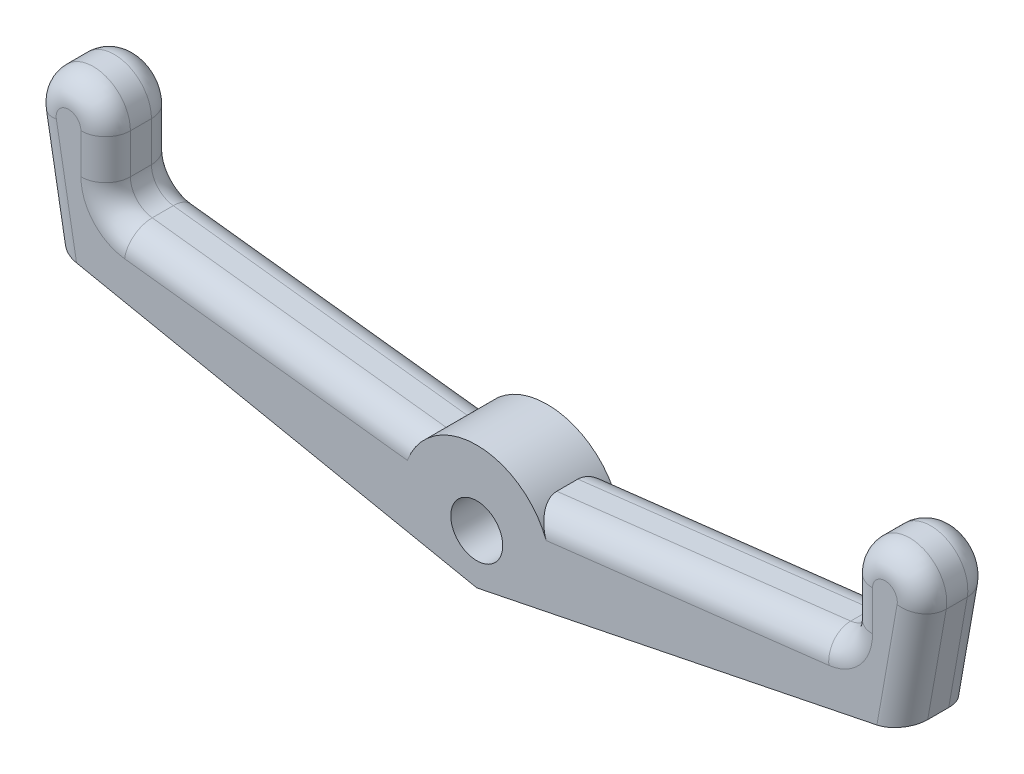
SolidWorks part; units mm, degrees
ref_plane "Front Plane" through (0, 0, 0) normal (0, 0, 1) x (1, 0, 0)
ref_plane "Top Plane" through (0, 0, 0) normal (0, 1, 0) x (1, 0, 0)
ref_plane "Right Plane" through (0, 0, 0) normal (1, 0, 0) x (0, 0, -1)
sketch "Sketch1" plane through (0, 0, 0) normal (0, 0, 1) x (1, 0, 0)
  line L0 (0, 0) -> (0, 4.534) construction
  line L1 (2.2361, 2) -> (15, 3.5)
  line L2 (15, 3.5) -> (15, 6)
  line L3 (17.9772, 5.7395) -> (17.2297, 1.5)
  line L4 (17.2297, 1.5) -> (0, -2)
  line L5 (-17.2297, 1.5) -> (0, -2)
  line L6 (-17.9772, 5.7395) -> (-17.2297, 1.5)
  line L7 (-15, 3.5) -> (-15, 6)
  line L8 (-2.2361, 2) -> (-15, 3.5)
  circle A0 centre (0, 0) radius 1.05
  arc A1 (15, 6) -> (17.9772, 5.7395) centre (16.5, 6) cw
  arc A2 (-2.2361, 2) -> (2.2361, 2) centre (0, 0) cw
  arc A3 (-15, 6) -> (-17.9772, 5.7395) centre (-16.5, 6) ccw
  dimension "D1" = 2.1
  dimension "D4" = 1.5
  dimension "D6" = 16.5
  dimension "D5" = 3
  dimension "D2" = 2
  dimension "D3" = 6
  dimension "D7" = 2.5
  dimension "D8" = 4.5
  dimension "D9" = 10
  dimension "D10" = 2
extrude "Boss-Extrude1" add sketch "Sketch1" along normal blind 2.85
fillet "Fillet2" radius 1 2 edges at (15, 3.5, 1.425) (-15, 3.5, 1.425)
fillet "Fillet1" radius 1 20 edges at (17.6034, 3.6198, 2.85) (15, 5.1947, 2.85) (17.6034, 3.6198, 0) (15, 5.1947, 0) (16.6307, 7.4943, 2.85) (16.6307, 7.4943, 0) (8.1764, 2.6981, 2.85) (14.7472, 3.7248, 2.85) (8.1764, 2.6981, 0) (14.7472, 3.7248, 0) (-8.1764, 2.6981, 0) (-14.7472, 3.7248, 0) (-15, 5.1947, 0) (-17.6034, 3.6198, 0) (-8.1764, 2.6981, 2.85) (-14.7472, 3.7248, 2.85) (-15, 5.1947, 2.85) (-17.6034, 3.6198, 2.85) (-16.6307, 7.4943, 0) (-16.6307, 7.4943, 2.85)
